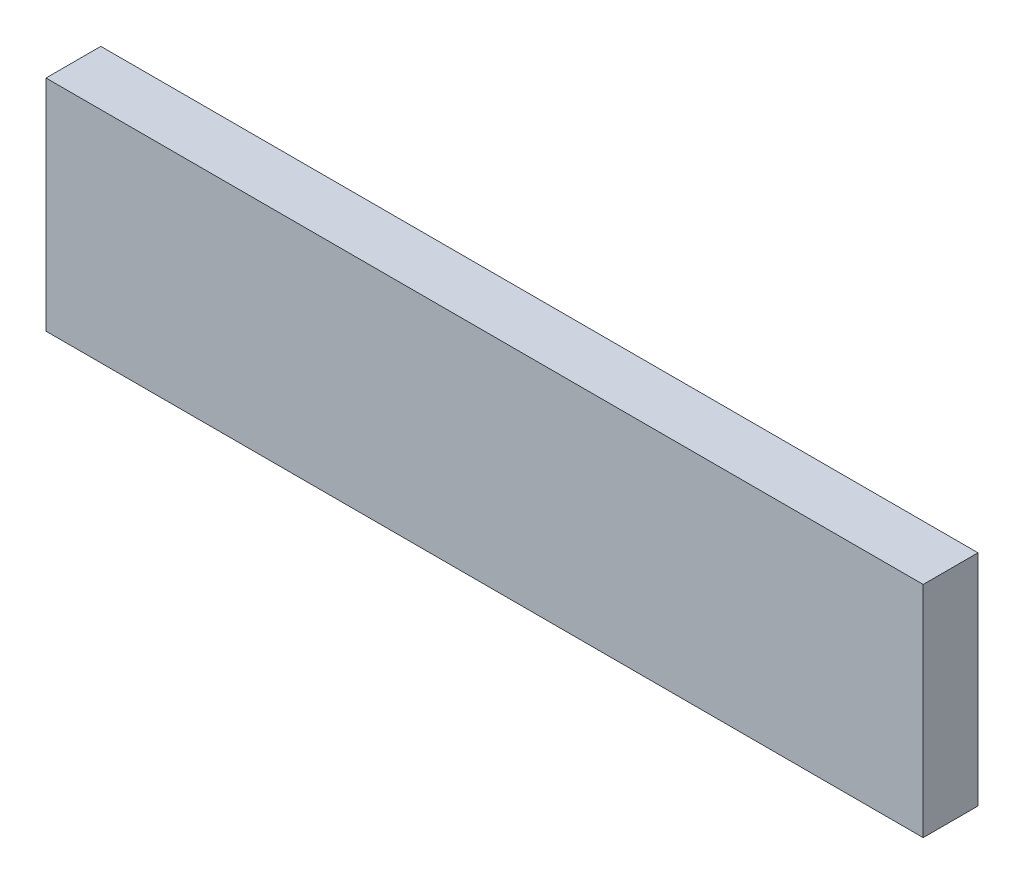
SolidWorks part; units mm, degrees
ref_plane "Front Plane" through (0, 0, 0) normal (0, 0, 1) x (1, 0, 0)
ref_plane "Top Plane" through (0, 0, 0) normal (0, 1, 0) x (1, 0, 0)
ref_plane "Right Plane" through (0, 0, 0) normal (1, 0, 0) x (0, 0, -1)
sketch "Sketch1" plane through (0, 0, 0) normal (0, 0, 1) x (1, 0, 0)
  line L1 (0, 0) -> (101.6, 0)
  line L2 (0, 0) -> (0, 25.4)
  line L3 (0, 25.4) -> (101.6, 25.4)
  line L4 (101.6, 0) -> (101.6, 25.4)
  dimension "D1" = 25.4
  dimension "D2" = 101.6
extrude "Extrude1" add sketch "Sketch1" against normal blind 6.35
